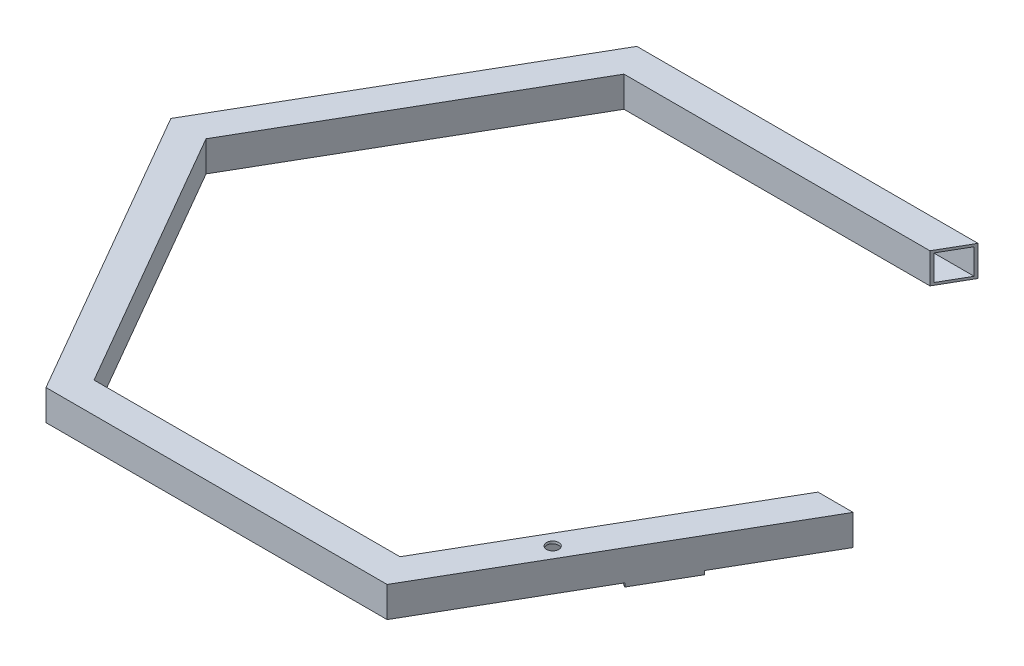
SolidWorks part; units mm, degrees
ref_plane "Front Plane" through (0, 0, 0) normal (0, 0, 1) x (1, 0, 0)
ref_plane "Top Plane" through (0, 0, 0) normal (0, 1, 0) x (1, 0, 0)
ref_plane "Right Plane" through (0, 0, 0) normal (1, 0, 0) x (0, 0, -1)
sketch "Sketch1" plane through (0, 0, 0) normal (0, 1, 0) x (1, 0, 0)
  line L0 (125.5662, 217.4871) -> (-125.5662, 217.4871)
  line L2 (140, 242.4871) -> (-140, 242.4871)
  line L3 (-140, 242.4871) -> (-280, 0)
  line L4 (-280, 0) -> (-140, -242.4871)
  line L5 (-140, -242.4871) -> (140, -242.4871)
  line L6 (140, -242.4871) -> (280, 0)
  line L7 (-125.5662, 217.4871) -> (-251.1325, 0)
  line L8 (-251.1325, 0) -> (-125.5662, -217.4871)
  line L9 (-125.5662, -217.4871) -> (125.5662, -217.4871)
  line L10 (125.5662, -217.4871) -> (251.1325, 0)
  line L12 (125.5662, 217.4871) -> (140, 242.4871)
  line L13 (251.1325, 0) -> (280, 0)
  line L14 (280, 0) -> (140, 242.4871) construction
  line L16 (251.1325, 0) -> (125.5662, 217.4871) construction
  line L17 (280, 0) -> (210, 121.2436) [skipped]
  arc A0 (107.235, 217.4871) -> (241.9669, -15.8753) centre (0, 0) ccw construction
  dimension "D1" = 280
  dimension "D2" = 25
extrude "Boss-Extrude1" add sketch "Sketch1" along normal blind 25
shell "Shell1" thickness 2
sketch "Sketch3" plane through (0, 25, 0) normal (0, 1, 0) x (1, 0, 0)
  line L0 (140, -242.4871) -> (280, 0) construction
  line L1 (168.1384, -168.75) -> (178.9637, -175) construction
  circle A0 centre (168.1384, -168.75) radius 7.1603 construction
  dimension "D1" = 12.5
  dimension "D2" = 175
sketch "Sketch4" plane through (0, 25, 0) normal (0, 1, 0) x (1, 0, 0)
  line L0 (140, -242.4871) -> (280, 0) construction
  circle A0 centre (180.5875, -147.1875) radius 5
  dimension "D1" = 10
  dimension "D2" = 12.5
extrude "Cut-Extrude2" cut sketch "Sketch4" against normal blind 40
sketch "Sketch5" plane through (0, 25, 0) normal (0, 1, 0) x (1, 0, 0)
  line L0 (201.1325, -86.6025) -> (159.2224, -159.1929)
  line L1 (201.1325, -86.6025) -> (140.5107, -51.6025)
  line L2 (159.2224, -159.1929) -> (98.6007, -124.1929)
  line L3 (140.5107, -51.6025) -> (98.6007, -124.1929)
  line L4 (251.1325, 0) -> (125.5662, -217.4871) construction
  circle A0 centre (121.2287, -125) radius 5.2115
  dimension "D1" = 100
  dimension "D2" = 70
  dimension "D3" = 50
  dimension "D4" = 125
extrude "Boss-Extrude2" add sketch "Sketch5" against normal blind 3
sketch "Sketch6" plane through (0, 25, 0) normal (0, 1, 0) x (1, 0, 0)
  line L0 (140.5107, -51.6025) -> (201.1325, -86.6025)
  line L1 (140.5107, -51.6025) -> (98.0612, -125.1273)
  line L2 (201.1325, -86.6025) -> (158.6829, -160.1273)
  line L3 (98.0612, -125.1273) -> (158.6829, -160.1273)
extrude "Cut-Extrude3" cut sketch "Sketch6" against normal blind 53
sketch "Sketch7" plane through (0, 25, 0) normal (0, 1, 0) x (1, 0, 0)
  line L0 (227.2976, -41.2833) -> (205.2976, -79.3884)
  line L1 (227.2976, -41.2833) -> (171.0059, -8.7833)
  line L2 (205.2976, -79.3884) -> (149.0059, -46.8884)
  line L3 (171.0059, -8.7833) -> (149.0059, -46.8884)
  line L4 (251.1325, 0) -> (125.5662, -217.4871) construction
  dimension "D1" = 44
  dimension "D2" = 65
extrude "Boss-Extrude3" add sketch "Sketch7" against normal blind 3 contours L2 L3 L1 L0
sketch "Sketch8" plane through (0, 25, 0) normal (0, 1, 0) x (1, 0, 0)
  line L0 (196.323, -78.9327) -> (265.5662, 0) construction
  line L1 (280, 0) -> (251.1325, 0) construction
  line L2 (140, -242.4871) -> (280, 0) construction
  circle A0 centre (196.323, -78.9327) radius 4.5966
  dimension "D1" = 33
  dimension "D2" = 105
extrude "Cut-Extrude4" cut sketch "Sketch8" against normal blind 3
sketch "Sketch9" plane through (0, 25, 0) normal (0, 1, 0) x (1, 0, 0)
  line L0 (205.2976, -79.3884) -> (200.1817, -76.4348)
  line L1 (205.2976, -79.3884) -> (194.3929, -98.2759)
  line L2 (149.0059, -46.8884) -> (138.1012, -65.7759)
  line L3 (194.3929, -98.2759) -> (138.1012, -65.7759)
  line L4 (196.557, -74.3421) -> (149.0059, -46.8884)
  arc A0 (196.557, -74.3421) -> (200.1817, -76.4348) centre (196.323, -78.9327) ccw
extrude "Boss-Extrude4" add sketch "Sketch9" against normal blind 3
sketch "Sketch10" plane through (0, 25, 0) normal (0, 1, 0) x (1, 0, 0)
  line L0 (171.0059, -8.7833) -> (227.2976, -41.2833)
  line L1 (171.0059, -8.7833) -> (154.9557, -36.5832)
  line L2 (227.2976, -41.2833) -> (211.2473, -69.0832)
  line L3 (154.9557, -36.5832) -> (211.2473, -69.0832)
  line L4 (227.2976, -41.2833) -> (171.0059, -8.7833) construction
  line L5 (171.0059, -8.7833) -> (138.1012, -65.7759) construction
extrude "Cut-Extrude5" cut sketch "Sketch10" against normal blind 3
sketch "Sketch11" plane through (0, 25, 0) normal (0, 1, 0) x (1, 0, 0)
  line L0 (154.9557, -36.5832) -> (189.3761, -56.4558)
  line L1 (154.9557, -36.5832) -> (138.2085, -65.59)
  line L2 (189.3761, -56.4558) -> (172.629, -85.4627)
  line L3 (138.2085, -65.59) -> (172.629, -85.4627)
  line L4 (154.9557, -36.5832) -> (211.2473, -69.0832) construction
extrude "Cut-Extrude6" cut sketch "Sketch11" against normal blind 3
sketch "Sketch12" plane through (0, 25, 0) normal (0, 1, 0) x (1, 0, 0)
  line L0 (133.473, -64.3276) -> (137.5058, -57.3178)
  line L1 (133.473, -64.3276) -> (171.9105, -86.4416)
  line L2 (137.5058, -57.3178) -> (175.9434, -79.4318)
  line L3 (171.9105, -86.4416) -> (175.9434, -79.4318)
extrude "Cut-Extrude7" cut sketch "Sketch12" against normal blind 3
sketch "Sketch13" plane through (0, 0, 0) normal (0, -1, 0) x (1, 0, 0)
  line L0 (197.9474, 92.1192) -> (189.7683, 106.2859)
  line L1 (176.0353, 79.3516) -> (189.3761, 56.4558)
  line L2 (189.3761, 56.4558) -> (211.2473, 69.0832)
  line L4 (251.1325, 0) -> (125.5662, 217.4871) construction
  line L5 (181.3198, 82.5192) -> (209.8194, 98.9734) construction
  line L6 (197.9474, 92.1192) -> (176.0353, 79.3516)
  line L7 (189.7683, 106.2859) -> (211.4189, 118.7859)
  line L8 (140, 242.4871) -> (280, 0) construction
  line L9 (211.4189, 118.7859) -> (235.3851, 77.2753)
  line L10 (235.3851, 77.2753) -> (213.403, 64.584)
  line L11 (207.8154, 74.2621) -> (220.3154, 52.6115) construction
  line L12 (213.403, 64.584) -> (211.2473, 69.0832)
extrude "Boss-Extrude5" add sketch "Sketch13" along normal blind 3
sketch "Sketch14" plane through (0, 0, 0) normal (0, 1, 0) x (1, 0, 0)
  circle A0 centre (192.705, -81.2228) radius 4.5966
extrude "Cut-Extrude8" cut sketch "Sketch14" against normal blind 23
sketch "Sketch15" plane through (0, 25, 0) normal (0, 1, 0) x (1, 0, 0)
  line L0 (187.4527, -55.3453) -> (211.2473, -69.0832)
  line L1 (211.2473, -69.0832) -> (194.3929, -98.2759)
  line L2 (194.3929, -98.2759) -> (170.3215, -84.3783)
  line L3 (170.3215, -84.3783) -> (187.4527, -55.3453)
extrude "Cut-Extrude10" cut sketch "Sketch15" against normal blind 23 contours L3 L0 L1 L2
